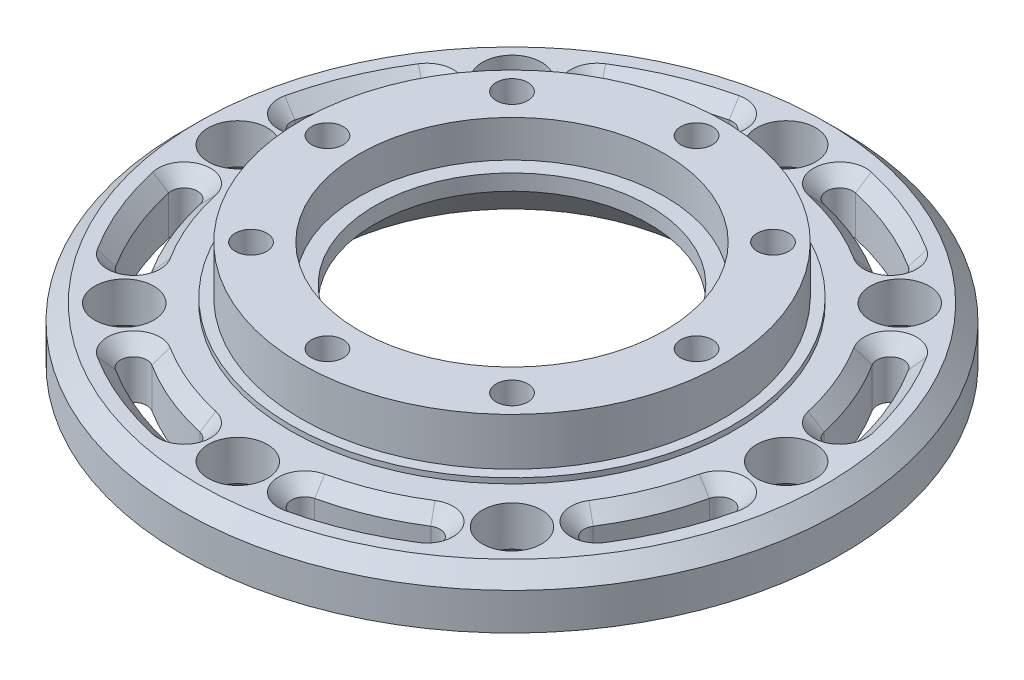
SolidWorks part; units mm, degrees
ref_plane "Front Plane" through (0, 0, 0) normal (0, 0, 1) x (1, 0, 0)
ref_plane "Top Plane" through (0, 0, 0) normal (0, 1, 0) x (1, 0, 0)
ref_plane "Right Plane" through (0, 0, 0) normal (1, 0, 0) x (0, 0, -1)
sketch "Sketch1" plane through (0, 0, 0) normal (0, 1, 0) x (1, 0, 0)
  circle A0 centre (0, 0) radius 52
  circle A1 centre (-52, 0) radius 5.5
  circle A2 centre (-36.7696, 36.7696) radius 5.5
  circle A3 centre (0, 52) radius 5.5
  circle A4 centre (36.7696, 36.7696) radius 5.5
  circle A5 centre (52, 0) radius 5.5
  circle A6 centre (36.7696, -36.7696) radius 5.5
  circle A7 centre (0, -52) radius 5.5
  circle A8 centre (-36.7696, -36.7696) radius 5.5
  circle A9 centre (0, 0) radius 41.5
  circle A10 centre (0, 0) radius 62.5
  point P21 (0, 0)
  dimension "D1" = 8
extrude "Boss-Extrude1" add sketch "Sketch1" along normal blind 10 contours A8 A0 A7 A6 A5 A4 A3 A2 A1 A9 | A10 A8 A0 A1 A2 A3 A4 A5 A6 A7
sketch "Sketch2" plane through (0, 10, 0) normal (0, 1, 0) x (1, 0, 0)
  line L0 (-40, 0) -> (-30, 0)
  circle A0 centre (0, 0) radius 40
  circle A1 centre (0, 0) radius 30
  circle A2 centre (-35, 0) radius 3.5
  circle A3 centre (-24.7487, 24.7487) radius 3.5
  circle A4 centre (0, 35) radius 3.5
  circle A5 centre (24.7487, 24.7487) radius 3.5
  circle A6 centre (35, 0) radius 3.5
  circle A7 centre (24.7487, -24.7487) radius 3.5
  circle A8 centre (0, -35) radius 3.5
  circle A9 centre (-24.7487, -24.7487) radius 3.5
  point P25 (0, 0)
  dimension "D1" = 8
extrude "Boss-Extrude2" add sketch "Sketch2" along normal mid plane 20
sketch "Sketch3" plane through (0, 20, 0) normal (0, 1, 0) x (1, 0, 0)
  circle A0 centre (-35, 0) radius 3.5
  circle A1 centre (-24.7487, 24.7487) radius 3.5
  circle A2 centre (0, 35) radius 3.5
  circle A3 centre (24.7487, 24.7487) radius 3.5
  circle A4 centre (35, 0) radius 3.5
  circle A5 centre (24.7487, -24.7487) radius 3.5
  circle A6 centre (0, -35) radius 3.5
  circle A7 centre (-24.7487, -24.7487) radius 3.5
  point P19 (0, 0)
  dimension "D1" = 8
extrude "Boss-Extrude3" add sketch "Sketch3" against normal blind 10 from offset 10 offset against normal yes
sketch "Sketch4" plane through (0, 20, 0) normal (0, 1, 0) x (1, 0, 0)
  circle A0 centre (0, 0) radius 40
  circle A1 centre (0, 0) radius 41.5
extrude "Cut-Extrude1" cut sketch "Sketch4" against normal blind 10
chamfer "Chamfer1" distance 3 angle 45 1 edges at (0, 10, 62.5)
sketch "Sketch9" plane through (0, 10, 0) normal (0, 1, 0) x (1, 0, 0)
  arc A1 (-51.0008, 10.1447) -> (-43.2364, 28.8897) centre (0, 0) cw construction
  arc A2 (-45.3151, 30.2786) -> (-53.4528, 10.6324) centre (0, 0) ccw
  arc A3 (-41.1577, 27.5007) -> (-48.5489, 9.657) centre (0, 0) ccw
  arc A4 (-41.1577, 27.5007) -> (-45.3151, 30.2786) centre (-43.2364, 28.8897) ccw
  arc A5 (-53.4528, 10.6324) -> (-48.5489, 9.657) centre (-51.0008, 10.1447) ccw
  arc A6 (-28.8897, 43.2364) -> (-10.1447, 51.0008) centre (0, 0) cw construction
  arc A7 (-10.6324, 53.4528) -> (-30.2786, 45.3151) centre (0, 0) ccw
  arc A8 (-9.657, 48.5489) -> (-27.5007, 41.1577) centre (0, 0) ccw
  arc A9 (-9.657, 48.5489) -> (-10.6324, 53.4528) centre (-10.1447, 51.0008) ccw
  arc A10 (-30.2786, 45.3151) -> (-27.5007, 41.1577) centre (-28.8897, 43.2364) ccw
  arc A11 (10.1447, 51.0008) -> (28.8897, 43.2364) centre (0, 0) cw construction
  arc A12 (30.2786, 45.3151) -> (10.6324, 53.4528) centre (0, 0) ccw
  arc A13 (27.5007, 41.1577) -> (9.657, 48.5489) centre (0, 0) ccw
  arc A14 (27.5007, 41.1577) -> (30.2786, 45.3151) centre (28.8897, 43.2364) ccw
  arc A15 (10.6324, 53.4528) -> (9.657, 48.5489) centre (10.1447, 51.0008) ccw
  arc A16 (43.2364, 28.8897) -> (51.0008, 10.1447) centre (0, 0) cw construction
  arc A17 (53.4528, 10.6324) -> (45.3151, 30.2786) centre (0, 0) ccw
  arc A18 (48.5489, 9.657) -> (41.1577, 27.5007) centre (0, 0) ccw
  arc A19 (48.5489, 9.657) -> (53.4528, 10.6324) centre (51.0008, 10.1447) ccw
  arc A20 (45.3151, 30.2786) -> (41.1577, 27.5007) centre (43.2364, 28.8897) ccw
  arc A21 (51.0008, -10.1447) -> (43.2364, -28.8897) centre (0, 0) cw construction
  arc A22 (45.3151, -30.2786) -> (53.4528, -10.6324) centre (0, 0) ccw
  arc A23 (41.1577, -27.5007) -> (48.5489, -9.657) centre (0, 0) ccw
  arc A24 (41.1577, -27.5007) -> (45.3151, -30.2786) centre (43.2364, -28.8897) ccw
  arc A25 (53.4528, -10.6324) -> (48.5489, -9.657) centre (51.0008, -10.1447) ccw
  arc A26 (28.8897, -43.2364) -> (10.1447, -51.0008) centre (0, 0) cw construction
  arc A27 (10.6324, -53.4528) -> (30.2786, -45.3151) centre (0, 0) ccw
  arc A28 (9.657, -48.5489) -> (27.5007, -41.1577) centre (0, 0) ccw
  arc A29 (9.657, -48.5489) -> (10.6324, -53.4528) centre (10.1447, -51.0008) ccw
  arc A30 (30.2786, -45.3151) -> (27.5007, -41.1577) centre (28.8897, -43.2364) ccw
  arc A31 (-10.1447, -51.0008) -> (-28.8897, -43.2364) centre (0, 0) cw construction
  arc A32 (-30.2786, -45.3151) -> (-10.6324, -53.4528) centre (0, 0) ccw
  arc A33 (-27.5007, -41.1577) -> (-9.657, -48.5489) centre (0, 0) ccw
  arc A34 (-27.5007, -41.1577) -> (-30.2786, -45.3151) centre (-28.8897, -43.2364) ccw
  arc A35 (-10.6324, -53.4528) -> (-9.657, -48.5489) centre (-10.1447, -51.0008) ccw
  arc A36 (-43.2364, -28.8897) -> (-51.0008, -10.1447) centre (0, 0) cw construction
  arc A37 (-53.4528, -10.6324) -> (-45.3151, -30.2786) centre (0, 0) ccw
  arc A38 (-48.5489, -9.657) -> (-41.1577, -27.5007) centre (0, 0) ccw
  arc A39 (-48.5489, -9.657) -> (-53.4528, -10.6324) centre (-51.0008, -10.1447) ccw
  arc A40 (-45.3151, -30.2786) -> (-41.1577, -27.5007) centre (-43.2364, -28.8897) ccw
  point P9 (-48.0417, 19.8995)
  point P14 (-19.8995, 48.0417)
  point P21 (19.8995, 48.0417)
  point P28 (48.0417, 19.8995)
  point P35 (48.0417, -19.8995)
  point P42 (19.8995, -48.0417)
  point P49 (-19.8995, -48.0417)
  point P56 (-48.0417, -19.8995)
  point P61 (0, 0)
  dimension "D1" = 8
extrude "Cut-Extrude4" cut sketch "Sketch9" against normal blind 13
sketch "Sketch10" plane through (0, 10, 0) normal (0, 1, 0) x (1, 0, 0)
  circle A0 centre (0, 0) radius 40
  circle A1 centre (0, 0) radius 42
extrude "Boss-Extrude4" add sketch "Sketch10" along normal blind 1
sketch "Sketch17" plane through (0, 10, 0) normal (0, 1, 0) x (1, 0, 0)
  arc A1 (-51.0008, 10.1447) -> (-43.2364, 28.8897) centre (0, 0) cw construction
  arc A2 (-45.3151, 30.2786) -> (-53.4528, 10.6324) centre (0, 0) ccw
  arc A3 (-41.1577, 27.5007) -> (-48.5489, 9.657) centre (0, 0) ccw
  arc A4 (-41.1577, 27.5007) -> (-45.3151, 30.2786) centre (-43.2364, 28.8897) ccw
  arc A5 (-53.4528, 10.6324) -> (-48.5489, 9.657) centre (-51.0008, 10.1447) ccw
  arc A6 (-28.8897, 43.2364) -> (-10.1447, 51.0008) centre (0, 0) cw construction
  arc A7 (-10.6324, 53.4528) -> (-30.2786, 45.3151) centre (0, 0) ccw
  arc A8 (-9.657, 48.5489) -> (-27.5007, 41.1577) centre (0, 0) ccw
  arc A9 (-9.657, 48.5489) -> (-10.6324, 53.4528) centre (-10.1447, 51.0008) ccw
  arc A10 (-30.2786, 45.3151) -> (-27.5007, 41.1577) centre (-28.8897, 43.2364) ccw
  arc A11 (10.1447, 51.0008) -> (28.8897, 43.2364) centre (0, 0) cw construction
  arc A12 (30.2786, 45.3151) -> (10.6324, 53.4528) centre (0, 0) ccw
  arc A13 (27.5007, 41.1577) -> (9.657, 48.5489) centre (0, 0) ccw
  arc A14 (27.5007, 41.1577) -> (30.2786, 45.3151) centre (28.8897, 43.2364) ccw
  arc A15 (10.6324, 53.4528) -> (9.657, 48.5489) centre (10.1447, 51.0008) ccw
  arc A16 (43.2364, 28.8897) -> (51.0008, 10.1447) centre (0, 0) cw construction
  arc A17 (53.4528, 10.6324) -> (45.3151, 30.2786) centre (0, 0) ccw
  arc A18 (48.5489, 9.657) -> (41.1577, 27.5007) centre (0, 0) ccw
  arc A19 (48.5489, 9.657) -> (53.4528, 10.6324) centre (51.0008, 10.1447) ccw
  arc A20 (45.3151, 30.2786) -> (41.1577, 27.5007) centre (43.2364, 28.8897) ccw
  arc A21 (51.0008, -10.1447) -> (43.2364, -28.8897) centre (0, 0) cw construction
  arc A22 (45.3151, -30.2786) -> (53.4528, -10.6324) centre (0, 0) ccw
  arc A23 (41.1577, -27.5007) -> (48.5489, -9.657) centre (0, 0) ccw
  arc A24 (41.1577, -27.5007) -> (45.3151, -30.2786) centre (43.2364, -28.8897) ccw
  arc A25 (53.4528, -10.6324) -> (48.5489, -9.657) centre (51.0008, -10.1447) ccw
  arc A26 (28.8897, -43.2364) -> (10.1447, -51.0008) centre (0, 0) cw construction
  arc A27 (10.6324, -53.4528) -> (30.2786, -45.3151) centre (0, 0) ccw
  arc A28 (9.657, -48.5489) -> (27.5007, -41.1577) centre (0, 0) ccw
  arc A29 (9.657, -48.5489) -> (10.6324, -53.4528) centre (10.1447, -51.0008) ccw
  arc A30 (30.2786, -45.3151) -> (27.5007, -41.1577) centre (28.8897, -43.2364) ccw
  arc A31 (-10.1447, -51.0008) -> (-28.8897, -43.2364) centre (0, 0) cw construction
  arc A32 (-30.2786, -45.3151) -> (-10.6324, -53.4528) centre (0, 0) ccw
  arc A33 (-27.5007, -41.1577) -> (-9.657, -48.5489) centre (0, 0) ccw
  arc A34 (-27.5007, -41.1577) -> (-30.2786, -45.3151) centre (-28.8897, -43.2364) ccw
  arc A35 (-10.6324, -53.4528) -> (-9.657, -48.5489) centre (-10.1447, -51.0008) ccw
  arc A36 (-43.2364, -28.8897) -> (-51.0008, -10.1447) centre (0, 0) cw construction
  arc A37 (-53.4528, -10.6324) -> (-45.3151, -30.2786) centre (0, 0) ccw
  arc A38 (-48.5489, -9.657) -> (-41.1577, -27.5007) centre (0, 0) ccw
  arc A39 (-48.5489, -9.657) -> (-53.4528, -10.6324) centre (-51.0008, -10.1447) ccw
  arc A40 (-45.3151, -30.2786) -> (-41.1577, -27.5007) centre (-43.2364, -28.8897) ccw
  point P7 (-48.0417, 19.8995)
  point P15 (-19.8995, 48.0417)
  point P22 (19.8995, 48.0417)
  point P29 (48.0417, 19.8995)
  point P36 (48.0417, -19.8995)
  point P43 (19.8995, -48.0417)
  point P50 (-19.8995, -48.0417)
  point P57 (-48.0417, -19.8995)
  point P62 (0, 0)
  dimension "D1" = 8
extrude "Boss-Extrude9" add sketch "Sketch17" against normal blind 10
chamfer "Chamfer7" distance 2.5 angle 45 8 edges at (0, 0, -46.5) (36.7696, 0, -31.2696) (52, 0, 5.5) (36.7696, 0, 42.2696) (0, 0, 57.5) (-36.7696, 0, 42.2696) (-52, 0, 5.5) (-36.7696, 0, -31.2696)
sketch "Sketch18" plane through (0, 10, 0) normal (0, 1, 0) x (1, 0, 0)
  circle A1 centre (0, 35) radius 3.5
  circle A2 centre (24.7487, 24.7487) radius 3.5
  circle A3 centre (35, 0) radius 3.5
  circle A4 centre (24.7487, -24.7487) radius 3.5
  circle A5 centre (0, -35) radius 3.5
  circle A6 centre (-24.7487, -24.7487) radius 3.5
  circle A7 centre (-35, 0) radius 3.5
  circle A8 centre (-24.7487, 24.7487) radius 3.5
  point P19 (0, 0)
  dimension "D1" = 8
extrude "Boss-Extrude10" add sketch "Sketch18" along normal blind 10
sketch "Sketch19" plane through (0, 20, 0) normal (0, 1, 0) x (1, 0, 0)
  line L0 (-30, 0) -> (-40, 0)
  circle A0 centre (0, 0) radius 30 construction
  circle A1 centre (0, 0) radius 40 construction
  circle A2 centre (-35, 0) radius 3
  circle A3 centre (-24.7487, 24.7487) radius 3
  circle A4 centre (0, 35) radius 3
  circle A5 centre (24.7487, 24.7487) radius 3
  circle A6 centre (35, 0) radius 3
  circle A7 centre (24.7487, -24.7487) radius 3
  circle A8 centre (0, -35) radius 3
  circle A9 centre (-24.7487, -24.7487) radius 3
  point P25 (0, 0)
  dimension "D1" = 8
extrude "Cut-Extrude7" cut sketch "Sketch19" against normal blind 5 contours A3 | A4 | A6 | A7 | A8 | A9 | L0 A2 | L0 A2 | A5
sketch "Sketch20" plane through (0, 10, 0) normal (0, 1, 0) x (1, 0, 0)
  arc A3 (-50.7284, 11.4295) -> (-43.9522, 27.7885) centre (0, 0) cw construction
  arc A4 (-46.0653, 29.1245) -> (-53.1672, 11.979) centre (0, 0) ccw
  arc A5 (-41.8391, 26.4525) -> (-48.2895, 10.88) centre (0, 0) ccw
  arc A6 (-41.8391, 26.4525) -> (-46.0653, 29.1245) centre (-43.9522, 27.7885) ccw
  arc A7 (-53.1672, 11.979) -> (-48.2895, 10.88) centre (-50.7284, 11.4295) ccw
  arc A8 (-27.7885, 43.9522) -> (-11.4295, 50.7284) centre (0, 0) cw construction
  arc A9 (-11.979, 53.1672) -> (-29.1245, 46.0653) centre (0, 0) ccw
  arc A10 (-10.88, 48.2895) -> (-26.4525, 41.8391) centre (0, 0) ccw
  arc A11 (-10.88, 48.2895) -> (-11.979, 53.1672) centre (-11.4295, 50.7284) ccw
  arc A12 (-29.1245, 46.0653) -> (-26.4525, 41.8391) centre (-27.7885, 43.9522) ccw
  arc A13 (11.4295, 50.7284) -> (27.7885, 43.9522) centre (0, 0) cw construction
  arc A14 (29.1245, 46.0653) -> (11.979, 53.1672) centre (0, 0) ccw
  arc A15 (26.4525, 41.8391) -> (10.88, 48.2895) centre (0, 0) ccw
  arc A16 (26.4525, 41.8391) -> (29.1245, 46.0653) centre (27.7885, 43.9522) ccw
  arc A17 (11.979, 53.1672) -> (10.88, 48.2895) centre (11.4295, 50.7284) ccw
  arc A18 (43.9522, 27.7885) -> (50.7284, 11.4295) centre (0, 0) cw construction
  arc A19 (53.1672, 11.979) -> (46.0653, 29.1245) centre (0, 0) ccw
  arc A20 (48.2895, 10.88) -> (41.8391, 26.4525) centre (0, 0) ccw
  arc A21 (48.2895, 10.88) -> (53.1672, 11.979) centre (50.7284, 11.4295) ccw
  arc A22 (46.0653, 29.1245) -> (41.8391, 26.4525) centre (43.9522, 27.7885) ccw
  arc A23 (50.7284, -11.4295) -> (43.9522, -27.7885) centre (0, 0) cw construction
  arc A24 (46.0653, -29.1245) -> (53.1672, -11.979) centre (0, 0) ccw
  arc A25 (41.8391, -26.4525) -> (48.2895, -10.88) centre (0, 0) ccw
  arc A26 (41.8391, -26.4525) -> (46.0653, -29.1245) centre (43.9522, -27.7885) ccw
  arc A27 (53.1672, -11.979) -> (48.2895, -10.88) centre (50.7284, -11.4295) ccw
  arc A28 (27.7885, -43.9522) -> (11.4295, -50.7284) centre (0, 0) cw construction
  arc A29 (11.979, -53.1672) -> (29.1245, -46.0653) centre (0, 0) ccw
  arc A30 (10.88, -48.2895) -> (26.4525, -41.8391) centre (0, 0) ccw
  arc A31 (10.88, -48.2895) -> (11.979, -53.1672) centre (11.4295, -50.7284) ccw
  arc A32 (29.1245, -46.0653) -> (26.4525, -41.8391) centre (27.7885, -43.9522) ccw
  arc A33 (-11.4295, -50.7284) -> (-27.7885, -43.9522) centre (0, 0) cw construction
  arc A34 (-29.1245, -46.0653) -> (-11.979, -53.1672) centre (0, 0) ccw
  arc A35 (-26.4525, -41.8391) -> (-10.88, -48.2895) centre (0, 0) ccw
  arc A36 (-26.4525, -41.8391) -> (-29.1245, -46.0653) centre (-27.7885, -43.9522) ccw
  arc A37 (-11.979, -53.1672) -> (-10.88, -48.2895) centre (-11.4295, -50.7284) ccw
  arc A38 (-43.9522, -27.7885) -> (-50.7284, -11.4295) centre (0, 0) cw construction
  arc A39 (-53.1672, -11.979) -> (-46.0653, -29.1245) centre (0, 0) ccw
  arc A40 (-48.2895, -10.88) -> (-41.8391, -26.4525) centre (0, 0) ccw
  arc A41 (-48.2895, -10.88) -> (-53.1672, -11.979) centre (-50.7284, -11.4295) ccw
  arc A42 (-46.0653, -29.1245) -> (-41.8391, -26.4525) centre (-43.9522, -27.7885) ccw
  point P11 (-48.0417, 19.8995)
  point P20 (-19.8995, 48.0417)
  point P27 (19.8995, 48.0417)
  point P34 (48.0417, 19.8995)
  point P41 (48.0417, -19.8995)
  point P48 (19.8995, -48.0417)
  point P55 (-19.8995, -48.0417)
  point P62 (-48.0417, -19.8995)
  point P67 (0, 0)
  dimension "D1" = 8
extrude "Cut-Extrude8" cut sketch "Sketch20" against normal blind 15
chamfer "Chamfer9" distance 2.5 angle 45 32 edges at (-50.3514, 10, 20.8562) (-42.6162, 10, 29.9016) (-51.2779, 10, 8.9906) (-45.732, 10, 18.9428) (-20.8562, 10, 50.3514) (-8.9906, 10, 51.2779) (-29.9016, 10, 42.6162) (-18.9428, 10, 45.732) (20.8562, 10, 50.3514) (29.9016, 10, 42.6162) (8.9906, 10, 51.2779) (18.9428, 10, 45.732) (50.3514, 10, 20.8562) (51.2779, 10, 8.9906) (42.6162, 10, 29.9016) (45.732, 10, 18.9428) (50.3514, 10, -20.8562) (42.6162, 10, -29.9016) (51.2779, 10, -8.9906) (45.732, 10, -18.9428) (20.8562, 10, -50.3514) (8.9906, 10, -51.2779) (29.9016, 10, -42.6162) (18.9428, 10, -45.732) (-20.8562, 10, -50.3514) (-29.9016, 10, -42.6162) (-8.9906, 10, -51.2779) (-18.9428, 10, -45.732) (-50.3514, 10, -20.8562) (-51.2779, 10, -8.9906) (-42.6162, 10, -29.9016) (-45.732, 10, -18.9428)
sketch "Sketch21" plane through (0, 10, 0) normal (0, 1, 0) x (1, 0, 0)
  circle A0 centre (-52, 0) radius 5.6
  circle A1 centre (-36.7696, 36.7696) radius 5.6
  circle A2 centre (0, 52) radius 5.6
  circle A3 centre (36.7696, 36.7696) radius 5.6
  circle A4 centre (52, 0) radius 5.6
  circle A5 centre (36.7696, -36.7696) radius 5.6
  circle A6 centre (0, -52) radius 5.6
  circle A7 centre (-36.7696, -36.7696) radius 5.6
  point P19 (0, 0)
  dimension "D1" = 8
extrude "Cut-Extrude9" cut sketch "Sketch21" against normal blind 15
sketch "Sketch22" plane through (0, 20, 0) normal (0, 1, 0) x (1, 0, 0)
  circle A0 centre (0, 0) radius 26
  circle A1 centre (0, 0) radius 30
extrude "Boss-Extrude11" add sketch "Sketch22" against normal blind 15 from offset 5 offset against normal yes
sketch "Sketch23" plane through (0, 15, 0) normal (0, 1, 0) x (1, 0, 0)
  circle A0 centre (0, 0) radius 29
  circle A1 centre (0, 0) radius 30
extrude "Boss-Extrude12" add sketch "Sketch23" along normal blind 5
chamfer "Chamfer10" distance 10 angle 45 1 edges at (0, 0, 26)
sketch "Sketch24" plane through (0, 15, 0) normal (0, 1, 0) x (1, 0, 0)
  circle A0 centre (0, 0) radius 29
  circle A1 centre (0, 0) radius 26
extrude "Cut-Extrude10" cut sketch "Sketch24" against normal blind 2
